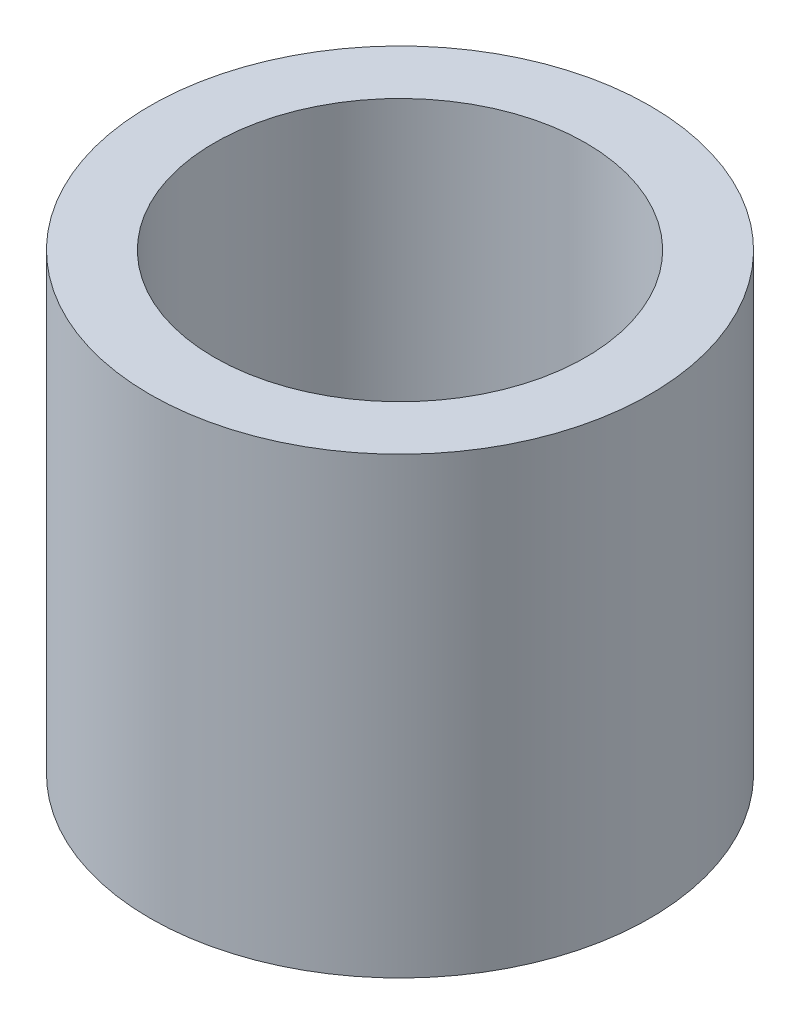
SolidWorks part; units mm, degrees
ref_plane "Front Plane" through (0, 0, 0) normal (0, 0, 1) x (1, 0, 0)
ref_plane "Top Plane" through (0, 0, 0) normal (0, 1, 0) x (1, 0, 0)
ref_plane "Right Plane" through (0, 0, 0) normal (1, 0, 0) x (0, 0, -1)
sketch "Sketch2" plane through (0, 0, 0) normal (0, 1, 0) x (1, 0, 0)
  circle A0 centre (0, 0) radius 3.5
  circle A1 centre (0, 0) radius 2.6
  dimension "D1" = 7
  dimension "D2" = 5.2
extrude "Boss-Extrude1" add sketch "Sketch2" along normal blind 6.35
